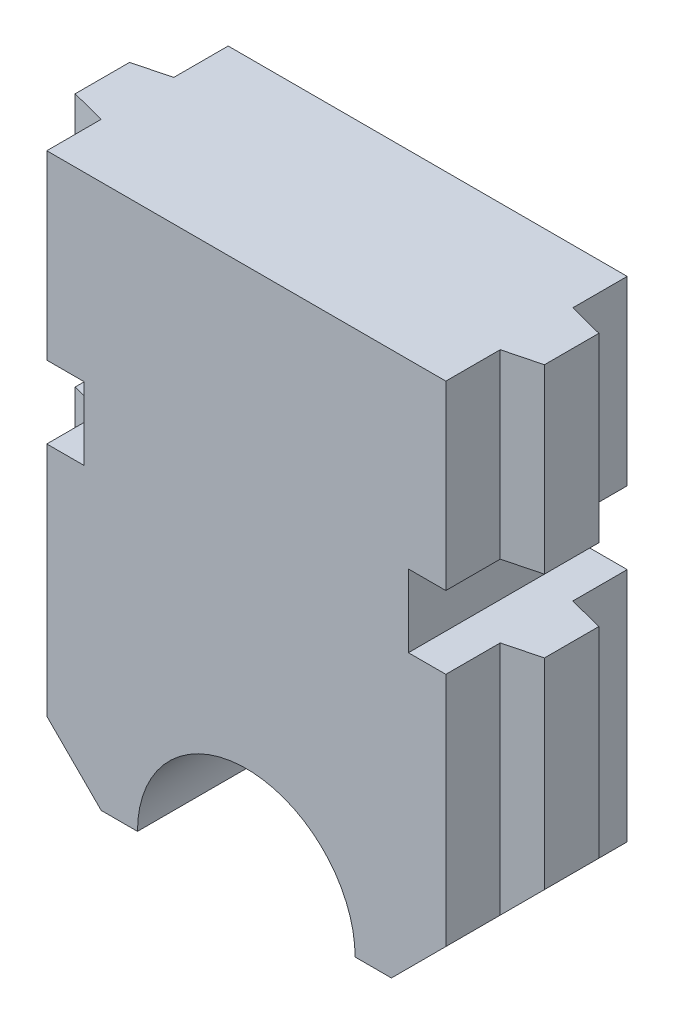
SolidWorks part; units mm, degrees
ref_plane "Front Plane" through (0, 0, 0) normal (0, 0, 1) x (1, 0, 0)
ref_plane "Top Plane" through (0, 0, 0) normal (0, 1, 0) x (1, 0, 0)
ref_plane "Right Plane" through (0, 0, 0) normal (1, 0, 0) x (0, 0, -1)
sketch "Sketch1" plane through (0, 0, 0) normal (0, 0, 1) x (1, 0, 0)
  line L0 (-19.8184, 19.7048) -> (-8.8184, 19.7048)
  line L1 (-8.8184, 19.7048) -> (-8.8184, 6.2048)
  line L2 (-8.8184, 6.2048) -> (-10.3184, 4.7048)
  line L3 (-10.3184, 4.7048) -> (-11.3184, 4.7048)
  line L4 (-19.8184, 19.7048) -> (-19.8184, 6.2048)
  line L5 (-19.8184, 6.2048) -> (-18.3184, 4.7048)
  line L6 (-18.3184, 4.7048) -> (-17.3184, 4.7048)
  arc A0 (-17.3184, 4.7048) -> (-11.3184, 4.7048) centre (-14.3184, 4.7048) cw
  dimension "D1" = 11
  dimension "D2" = 13.5
  dimension "D3" = 13.5
  dimension "D4" = 1
  dimension "D5" = 1
  dimension "D6" = 1.5
  dimension "D7" = 1.5
  dimension "D8" = 1.5
extrude "Boss-Extrude1" add sketch "Sketch1" along normal blind 5 contours L4 L5 L6 A0 L3 L2 L1 L0
sketch "Sketch2" plane through (0, 19.7048, 0) normal (0, 1, 0) x (1, 0, 0)
  line L0 (-19.8184, -1.5) -> (-8.8184, -1.5)
  line L2 (-8.8184, -5) -> (-8.8184, 0) construction
  line L3 (-8.8184, -3.5) -> (-19.8184, -3.5)
  line L4 (-8.8184, -1.5) -> (-7.8502, -1.75)
  line L5 (-19.8184, -3.5) -> (-19.8525, -3.5042)
  line L6 (-7.8502, -3.25) -> (-7.8502, -1.75)
  line L7 (-8.8184, -3.5) -> (-7.8502, -3.25)
  line L8 (-14.3184, 0) -> (-14.3184, -5) construction
  line L9 (-19.8184, 0) -> (-8.8184, 0) construction
  line L10 (-19.8184, -5) -> (-8.8184, -5) construction
  line L11 (-19.8184, -3.5) -> (-20.7867, -3.25)
  line L12 (-20.7867, -3.25) -> (-20.7867, -1.75)
  line L13 (-19.8184, -1.5) -> (-20.7867, -1.75)
  dimension "D2" = 1
extrude "Boss-Extrude2" add sketch "Sketch2" against normal blind 15 contours L11 L12 L13 L0 L4 L6 L7 L3
sketch "Sketch3" plane through (0, 0, 5) normal (0, 0, 1) x (1, 0, 0)
  line L0 (-18.3184, 4.7048) -> (-20.7867, 7.1731)
  line L1 (-20.7867, 4.7048) -> (-20.7867, 19.7048) construction
  line L2 (-20.7867, 7.1731) -> (-20.7867, 3.7096)
  line L3 (-18.3184, 4.7048) -> (-17.3184, 4.7048)
  line L4 (-11.3184, 4.7048) -> (-10.3184, 4.7048)
  line L5 (-10.3184, 4.7048) -> (-7.8502, 7.1731)
  line L6 (-7.8502, 4.7048) -> (-7.8502, 19.7048) construction
  line L7 (-7.8502, 7.1731) -> (-7.8502, 3.7096)
  line L8 (-7.8502, 3.7096) -> (-20.7867, 3.7096)
  arc A0 (-17.3184, 4.7048) -> (-11.3184, 4.7048) centre (-14.3184, 4.7048) cw
extrude "Cut-Extrude1" cut sketch "Sketch3" against normal blind 15
sketch "Sketch4" plane through (0, 0, 5) normal (0, 0, 1) x (1, 0, 0)
  line L0 (-14.3184, 19.7048) -> (-14.3184, 14.7048) construction
  line L1 (-19.8184, 19.7048) -> (-8.8184, 19.7048) construction
  line L2 (-14.3184, 14.7048) -> (-14.3184, 12.7048) construction
  line L3 (-14.3184, 14.7048) -> (-20.7867, 14.7048) construction
  line L4 (-20.7867, 7.1731) -> (-20.7867, 19.7048) construction
  line L5 (-20.7867, 14.7048) -> (-20.7867, 12.7048) construction
  line L6 (-20.7867, 12.7048) -> (-14.3184, 12.7048) construction
  line L7 (-20.7867, 14.7048) -> (-18.7867, 14.7048)
  line L8 (-18.7867, 14.7048) -> (-18.7867, 12.7048)
  line L9 (-18.7867, 12.7048) -> (-20.7867, 12.7048)
  line L10 (-20.7867, 12.7048) -> (-20.7867, 14.7048)
  dimension "D1" = 5
  dimension "D2" = 2
  dimension "D3" = 2
sketch "Sketch5" plane through (0, 19.7048, 0) normal (0, 1, 0) x (1, 0, 0)
  line L0 (-14.3184, -5) -> (-14.3184, 0) construction
  line L1 (-19.8184, 0) -> (-8.8184, 0) construction
ref_plane "Plane1" through (-14.3184, 0, 0) normal (1, 0, 0) x (0, 0, -1)
extrude "Cut-Extrude2" cut sketch "Sketch4" against normal blind 15 contours L7 L8 L9 L10
mirror "Mirror1" about plane through (-14.3184, 0, 0) normal (1, 0, 0) of "Cut-Extrude2"
